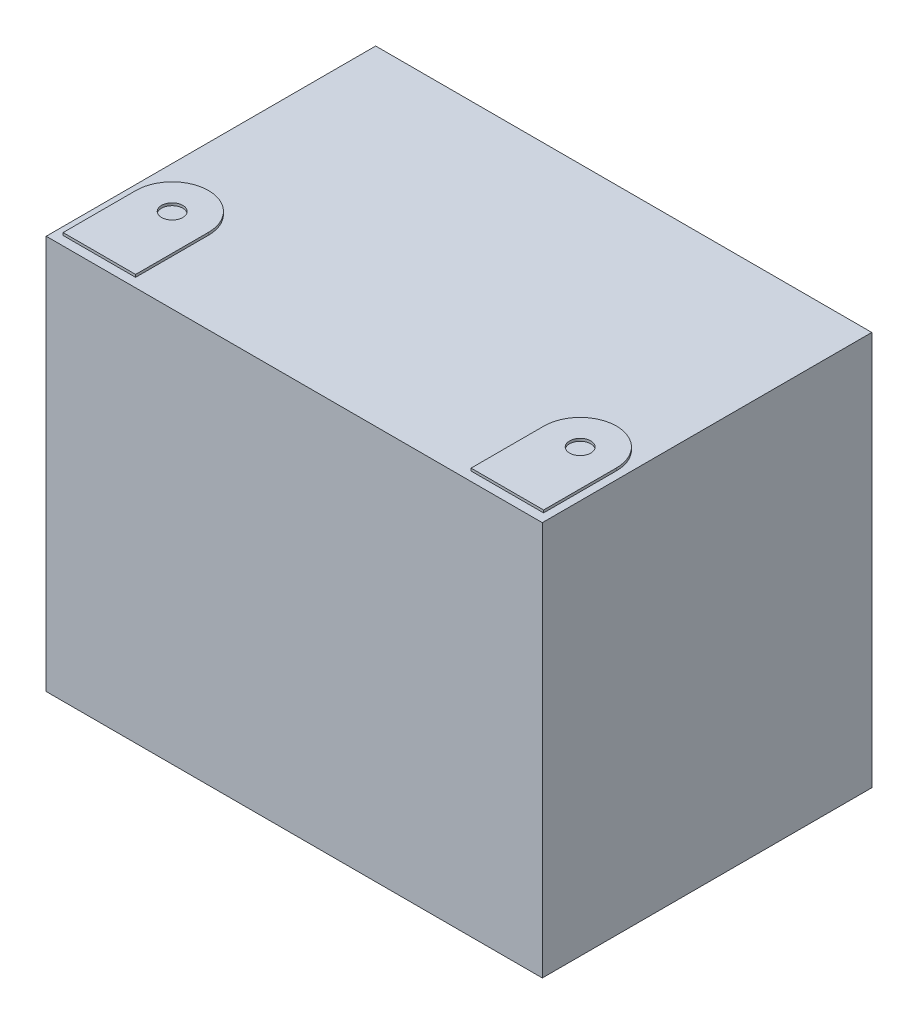
SolidWorks part; units mm, degrees
ref_plane "Front Plane" through (0, 0, 0) normal (0, 0, 1) x (1, 0, 0)
ref_plane "Top Plane" through (0, 0, 0) normal (0, 1, 0) x (1, 0, 0)
ref_plane "Right Plane" through (0, 0, 0) normal (1, 0, 0) x (0, 0, -1)
sketch "Sketch1" plane through (0, 0, 0) normal (0, 1, 0) x (1, 0, 0)
  line L1 (-97.5, 64.75) -> (97.5, 64.75)
  line L2 (-97.5, 64.75) -> (-97.5, -64.75)
  line L3 (-97.5, -64.75) -> (97.5, -64.75)
  line L4 (97.5, 64.75) -> (97.5, -64.75)
  line L5 (-97.5, 64.75) -> (97.5, -64.75) construction
  line L6 (-97.5, -64.75) -> (97.5, 64.75) construction
  point P0 (0, 0)
  dimension "D1" = 195
  dimension "D2" = 129.5
extrude "Boss-Extrude1" add sketch "Sketch1" against normal blind 155
sketch "Sketch2" plane through (0, 0, 0) normal (0, 1, 0) x (1, 0, 0)
  line L0 (-94.4338, -61.1813) -> (-65.9338, -61.1813)
  line L1 (-94.4338, -61.1813) -> (-94.4338, -32.5467)
  line L2 (-65.9338, -61.1813) -> (-65.9338, -32.5467)
  line L3 (-80.1838, -61.1813) -> (-80.1838, -32.5467) construction
  arc A0 (-94.4338, -32.5467) -> (-65.9338, -32.5467) centre (-80.1838, -32.5467) cw
  circle A1 centre (-80.1838, -32.5467) radius 4.1641
  point P6 (0, 0)
  point P7 (0, 0)
  point P9 (-94.4338, -61.1813)
  dimension "D3" = 14.25
  dimension "D1" = 28.5
  dimension "D2" = 28.6346
extrude "Boss-Extrude2" add sketch "Sketch2" along normal blind 1
mirror "Mirror1" about plane through (0, 0, 0) normal (1, 0, 0) of "Boss-Extrude2"
